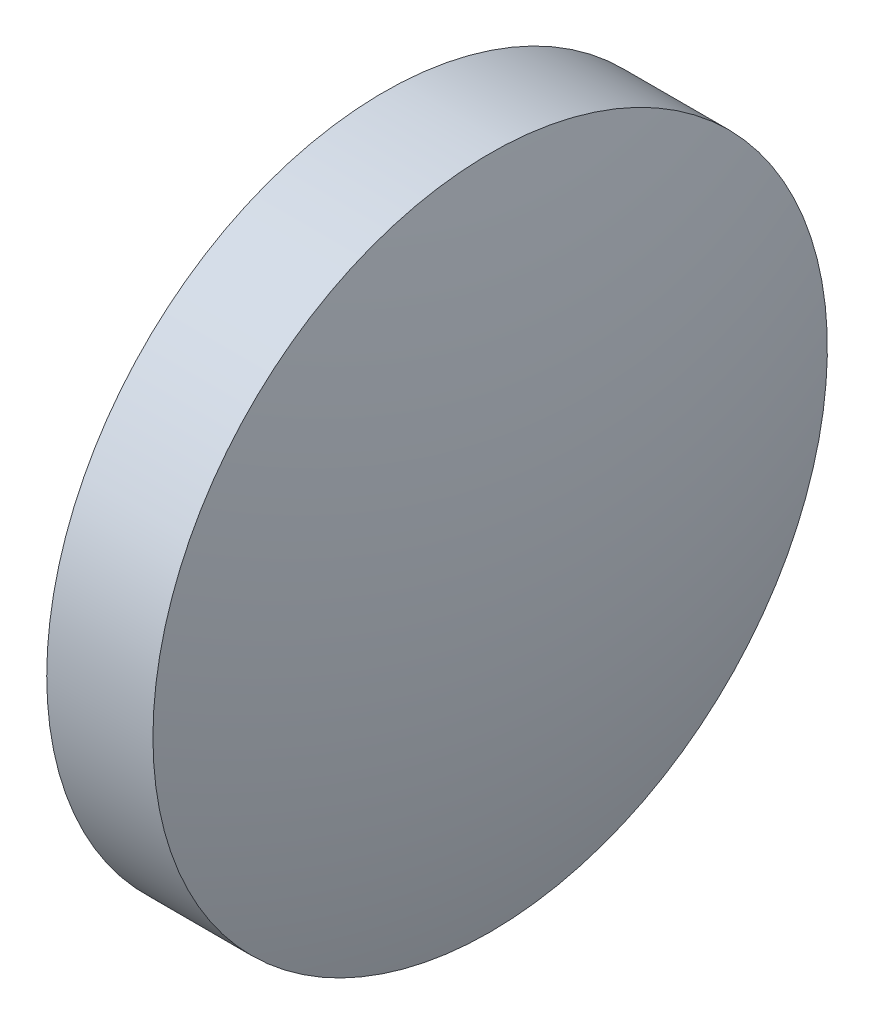
SolidWorks part; units mm, degrees
ref_plane "前视基准面" through (0, 0, 0) normal (0, 0, 1) x (1, 0, 0)
ref_plane "上视基准面" through (0, 0, 0) normal (0, 1, 0) x (1, 0, 0)
ref_plane "右视基准面" through (0, 0, 0) normal (1, 0, 0) x (0, 0, -1)
sketch "草图1" plane through (0, 0, 0) normal (0, 0, 1) x (1, 0, 0)
  line L0 (438.3993, -5.1295) -> (449.7026, -5.1295) construction
  line L1 (440.7273, -5.1295) -> (440.7273, 1.2205)
  line L2 (440.7273, 1.2205) -> (442.7273, 1.2205)
  line L3 (443.6273, -5.1295) -> (440.7273, -5.1295)
  arc A0 (443.6273, -5.1295) -> (442.7273, 1.2205) centre (420.7759, -5.1295) ccw
revolve "旋转1" add sketch "草图1" angle 360 about L0
